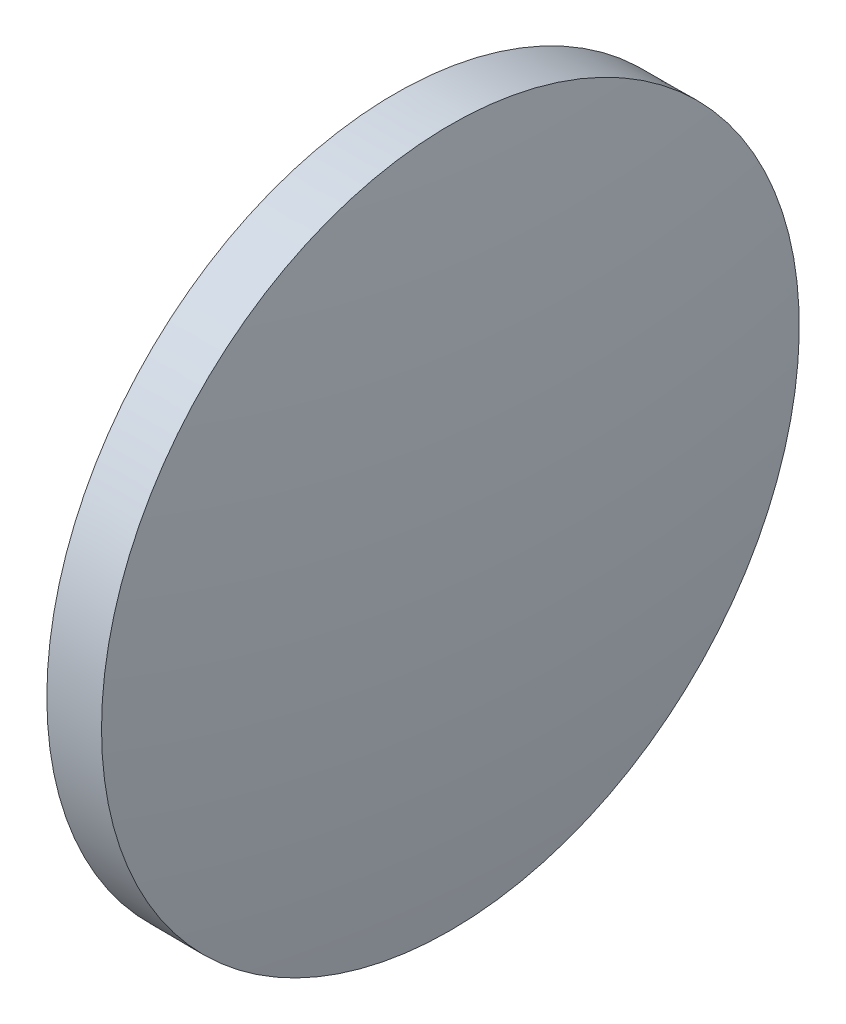
SolidWorks part; units mm, degrees
ref_plane "前视基准面" through (0, 0, 0) normal (0, 0, 1) x (1, 0, 0)
ref_plane "上视基准面" through (0, 0, 0) normal (0, 1, 0) x (1, 0, 0)
ref_plane "右视基准面" through (0, 0, 0) normal (1, 0, 0) x (0, 0, -1)
sketch "草图1" plane through (0, 0, 0) normal (0, 0, 1) x (1, 0, 0)
  line L0 (79.3315, 48.6321) -> (93.5079, 48.6321) construction
  line L1 (85.4866, 61.3279) -> (87.4866, 61.3363)
  line L2 (87.4866, 61.3363) -> (87.4866, 35.9279)
  line L3 (87.4866, 35.9279) -> (85.4866, 35.9279)
  line L4 (85.4866, 35.9279) -> (85.4866, 61.3279)
  arc A0 (85.4866, 61.3279) -> (85.4866, 35.9279) centre (169.9005, 48.6279) ccw
  arc A1 (87.4866, 35.9279) -> (87.4866, 61.3363) centre (3.0734, 48.6321) ccw
  dimension "D1" = 2
  dimension "D2" = 25.4
revolve "旋转1" add sketch "草图1" angle 360 about L0
